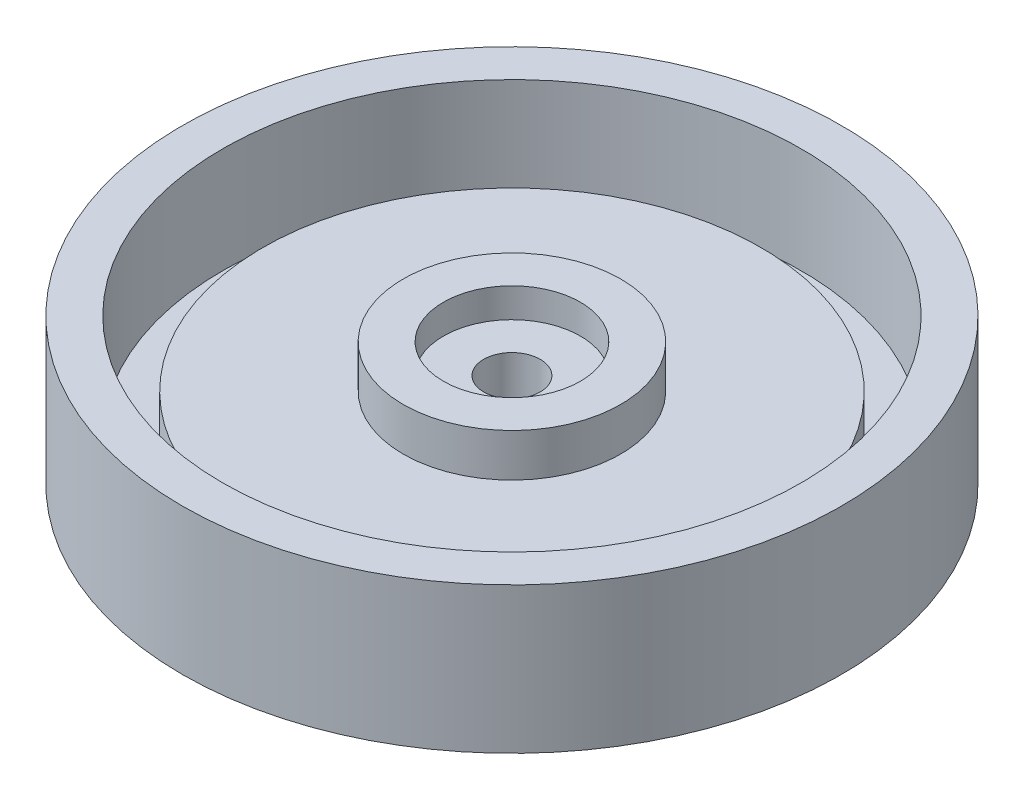
SolidWorks part; units mm, degrees
ref_plane "Piano frontale" through (0, 0, 0) normal (0, 0, 1) x (1, 0, 0)
ref_plane "Piano superiore" through (0, 0, 0) normal (0, 1, 0) x (1, 0, 0)
ref_plane "Piano destro" through (0, 0, 0) normal (1, 0, 0) x (0, 0, -1)
sketch "Schizzo3" plane through (0, 0, 0) normal (0, 0, 1) x (1, 0, 0)
  line L0 (0, -9.367) -> (35.2784, -9.367)
  line L1 (0, -55) -> (0, 55) construction
  line L2 (35.2784, -9.367) -> (35.2784, 0)
  line L3 (55, 0) -> (-55, 0) construction
  line L4 (35.2784, 0) -> (73.7155, 0)
  line L5 (73.7155, 0) -> (73.7155, 32.633)
  line L6 (73.7155, 32.633) -> (64.7155, 32.633)
  line L7 (64.7155, 32.633) -> (64.7155, 9)
  line L8 (64.7155, 9) -> (55.7155, 9)
  line L9 (55.7155, 9) -> (55.7155, 18)
  line L10 (55.7155, 18) -> (24.3258, 18)
  line L11 (24.3258, 18) -> (24.3258, 27.6145)
  line L12 (24.3258, 27.6145) -> (15.3258, 27.6145)
  line L13 (15.3258, 27.6145) -> (15.3258, 21.0454)
  line L14 (6.3258, 21.0454) -> (15.3258, 21.0454)
  line L15 (6.3258, 21.0454) -> (6.3258, 0)
  line L16 (6.3258, 0) -> (0, 0)
  line L17 (0, 0) -> (0, -9.367)
  line L18 (0, 108.1618) -> (0, -99.5653) construction
  point P10 (15.3258, 24.3299)
  dimension "D1" = 9
  dimension "D2" = 9
  dimension "D3" = 9
  dimension "D4" = 9
  dimension "D5" = 9
  dimension "D6" = 42
  dimension "D7" = 9
  dimension "D8" = 73.7155
  dimension "D9" = 32.633
  dimension "D10" = 21.0454
  dimension "D11" = 49.3897
  dimension "D12" = 36.9815
  dimension "D13" = 35.2784
revolve "Rivoluzione1" add sketch "Schizzo3" angle 360 about L18
